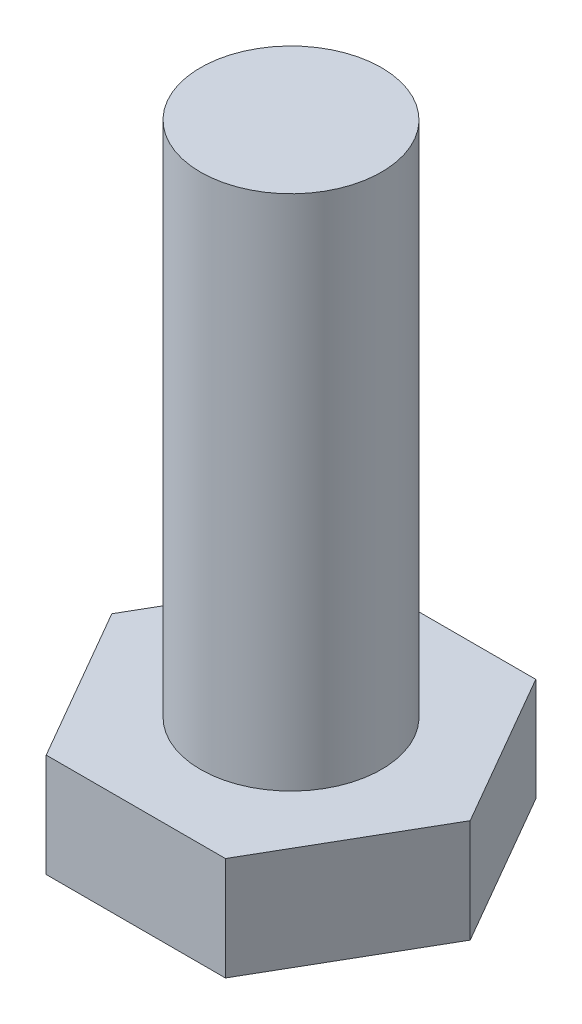
SolidWorks part; units mm, degrees
ref_plane "Front Plane" through (0, 0, 0) normal (0, 0, 1) x (1, 0, 0)
ref_plane "Top Plane" through (0, 0, 0) normal (0, 1, 0) x (1, 0, 0)
ref_plane "Right Plane" through (0, 0, 0) normal (1, 0, 0) x (0, 0, -1)
sketch "Sketch1" plane through (0, 0, 0) normal (0, 1, 0) x (1, 0, 0)
  line L1 (1.7321, 3) -> (-1.7321, 3)
  line L2 (-1.7321, 3) -> (-3.4641, 0)
  line L3 (-3.4641, 0) -> (-1.7321, -3)
  line L4 (-1.7321, -3) -> (1.7321, -3)
  line L5 (1.7321, -3) -> (3.4641, 0)
  line L6 (3.4641, 0) -> (1.7321, 3)
  circle A0 centre (0, 0) radius 3 construction
  circle A1 centre (0, 0) radius 1.75 construction
  dimension "D1" = 3.5
  dimension "D2" = 6
extrude "Boss-Extrude1" add sketch "Sketch1" along normal blind 2 contours L2 L3 L4 L5 L6 L1
sketch "Sketch2" plane through (0, 2, 0) normal (0, 1, 0) x (1, 0, 0)
  circle A0 centre (0, 0) radius 1.75
  dimension "D1" = 3.5
extrude "Boss-Extrude2" add sketch "Sketch2" along normal blind 10
